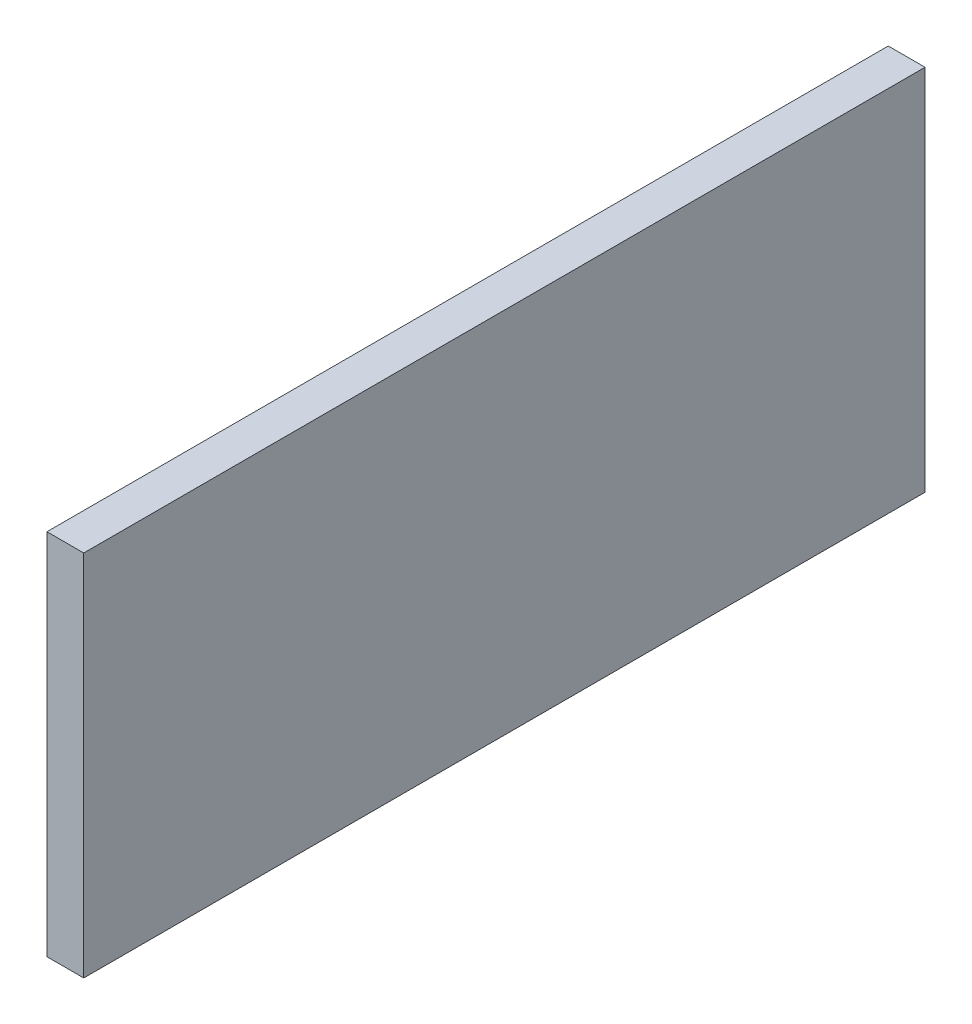
SolidWorks part; units mm, degrees
ref_plane "Front Plane" through (0, 0, 0) normal (0, 0, 1) x (1, 0, 0)
ref_plane "Top Plane" through (0, 0, 0) normal (0, 1, 0) x (1, 0, 0)
ref_plane "Right Plane" through (0, 0, 0) normal (1, 0, 0) x (0, 0, -1)
sketch "Sketch1" plane through (0, 0, 0) normal (1, 0, 0) x (0, 0, -1)
  line L1 (-80, 35) -> (80, 35)
  line L2 (-80, 35) -> (-80, -35)
  line L3 (-80, -35) -> (80, -35)
  line L4 (80, 35) -> (80, -35)
  line L5 (-80, 35) -> (80, -35) construction
  line L6 (-80, -35) -> (80, 35) construction
  point P0 (0, 0)
  dimension "D1" = 70
  dimension "D2" = 160
extrude "Boss-Extrude1" add sketch "Sketch1" along normal blind 7
